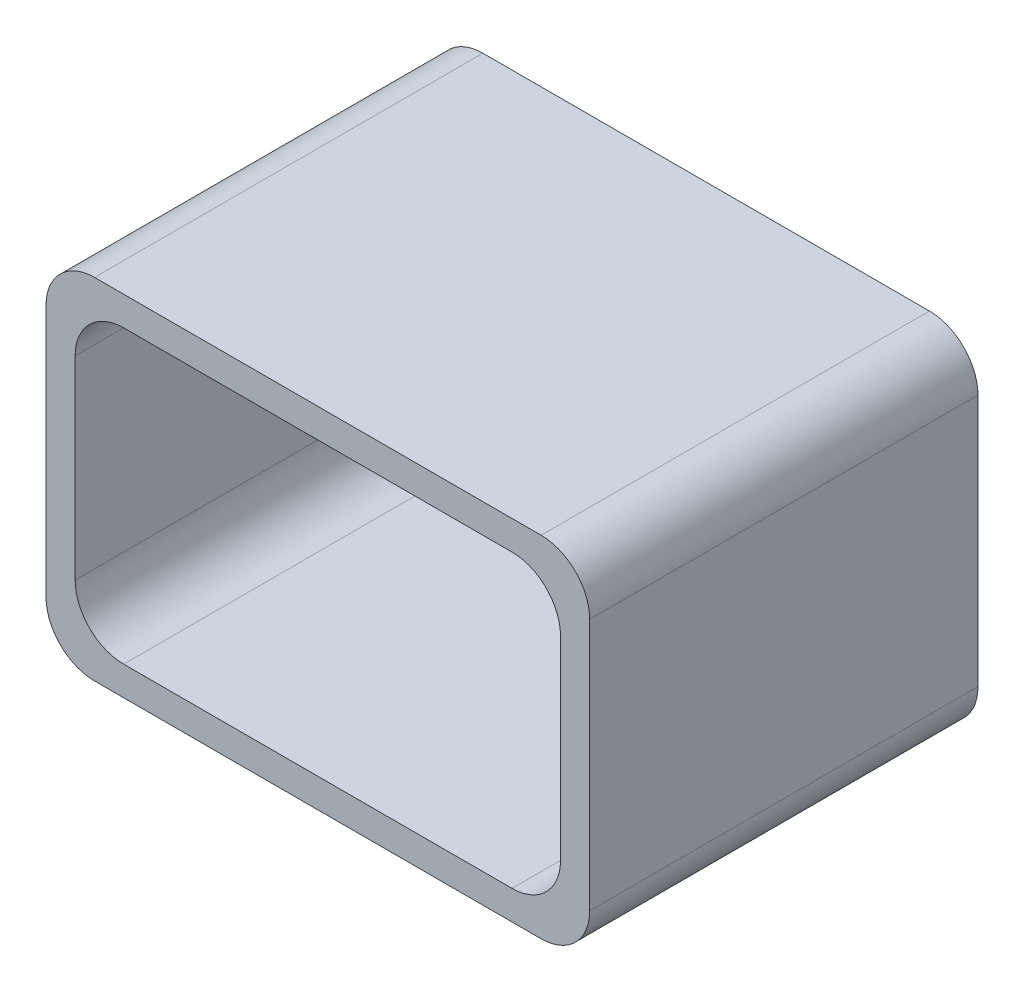
SolidWorks part; units mm, degrees
ref_plane "Front Plane" through (0, 0, 0) normal (0, 0, 1) x (1, 0, 0)
ref_plane "Top Plane" through (0, 0, 0) normal (0, 1, 0) x (1, 0, 0)
ref_plane "Right Plane" through (0, 0, 0) normal (1, 0, 0) x (0, 0, -1)
sketch "Sketch1" plane through (0, 0, 0) normal (0, 0, 1) x (1, 0, 0)
  line L1 (0, 0) -> (0.56, 0)
  line L2 (0, 0) -> (0, 0.36)
  line L3 (0, 0.36) -> (0.56, 0.36)
  line L4 (0.56, 0) -> (0.56, 0.36)
  line L5 (0.03, 0.33) -> (0.53, 0.33)
  line L6 (0.03, 0.33) -> (0.03, 0.03)
  line L7 (0.03, 0.03) -> (0.53, 0.03)
  line L8 (0.53, 0.33) -> (0.53, 0.03)
  point P9 (0.28, 0.36)
  point P10 (0.28, 0.33)
  point P11 (0.53, 0.18)
  point P12 (0.56, 0.18)
  dimension "D1" = 0.56
  dimension "D2" = 0.36
  dimension "D3" = 0.03
  dimension "D4" = 0.03
extrude "Boss-Extrude1" add sketch "Sketch1" along normal blind 0.4
fillet "Fillet1" radius 0.05 8 edges at (0.56, 0, 0.2) (0, 0, 0.2) (0.56, 0.36, 0.2) (0, 0.36, 0.2) (0.53, 0.03, 0.2) (0.53, 0.33, 0.2) (0.03, 0.03, 0.2) (0.03, 0.33, 0.2)
